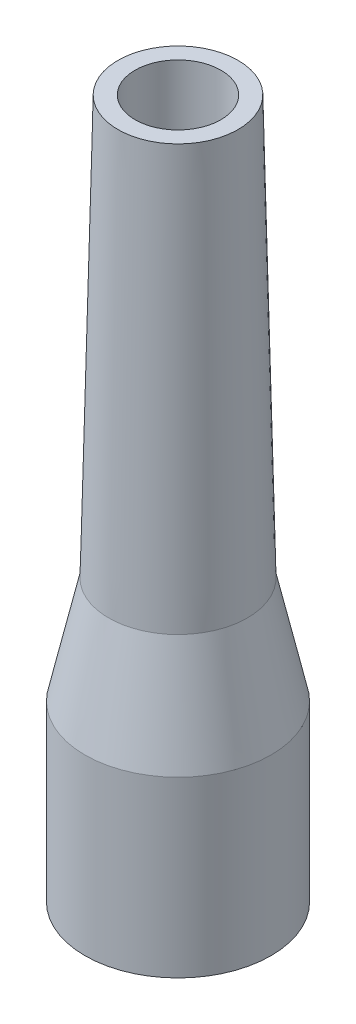
SolidWorks part; units mm, degrees
ref_plane "Front Plane" through (0, 0, 0) normal (0, 0, 1) x (1, 0, 0)
ref_plane "Top Plane" through (0, 0, 0) normal (0, 1, 0) x (1, 0, 0)
ref_plane "Right Plane" through (0, 0, 0) normal (1, 0, 0) x (0, 0, -1)
sketch "Sketch1" plane through (0, 0, 0) normal (1, 0, 0) x (0, 0, -1)
  line L0 (0, 0) -> (0, 38.8884) construction
  line L1 (0, 38.8884) -> (-4.9, 38.8884) construction
  line L2 (-4.9, 38.8884) -> (-5.85, 0) construction
  line L3 (-5, 38.8908) -> (-5.95, 0.0024)
  line L5 (-5, 38.8908) -> (-3.9, 43.8525)
  line L6 (-5.95, 0.0024) -> (-8.45, 0.0024)
  line L7 (-6.4, 25.4934) -> (-5.55, 63.4839) construction
  line L8 (-5.55, 63.4839) -> (0, 63.4839) construction
  line L9 (0, 63.4839) -> (0, 38.8884) construction
  line L10 (-6.3, 25.4912) -> (-5.45, 63.4817)
  line L11 (-6.3, 25.4912) -> (-5.45, 63.4817) construction
  line L12 (-8.45, 0.0024) -> (-8.45, 15.7934)
  line L13 (-3.9, 63.4817) -> (-5.45, 63.4817)
  line L14 (-5.55, 63.4839) -> (-5.45, 63.4817) construction
  line L15 (-6.4, 25.4934) -> (-6.3, 25.4912) construction
  line L16 (-5, 38.8908) -> (-5.9997, 38.9132) construction
  line L17 (-8.45, 15.7934) -> (-6.3, 25.4912)
  line L18 (-3.9, 43.8525) -> (-3.9, 63.4817)
  point P8 (-8.0329, 22.0103)
  point P15 (-7.3336, 21.5846)
  point P16 (-5, 43.0901)
  point P22 (-4.5953, 42.9683)
  dimension "D1" = 38.9
  dimension "D2" = 9.8
  dimension "D3" = 11.7
  dimension "D6" = 11.1
  dimension "D7" = 38
  dimension "D8" = 12.8
  dimension "D5" = 1
  dimension "D10" = 12.5
  dimension "D11" = 2.5
  dimension "D12" = 12.5
  dimension "D13" = 7.8
  dimension "D4" = 0.1
  dimension "D9" = 0.1
revolve "Revolve1" add sketch "Sketch1" angle 360 about L0
equation "\"Tolerance\"=0.1"
equation "\"D4@Sketch1\"=\"Tolerance\""
equation "\"D9@Sketch1\"=\"Tolerance\""
